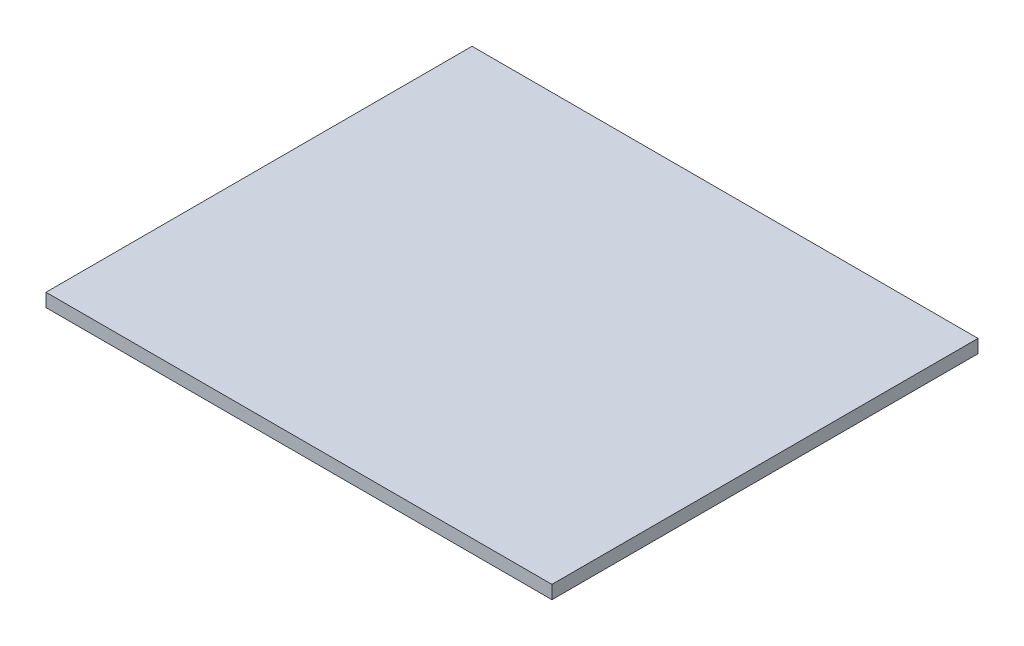
SolidWorks part; units mm, degrees
ref_plane "Front Plane" through (0, 0, 0) normal (0, 0, 1) x (1, 0, 0)
ref_plane "Top Plane" through (0, 0, 0) normal (0, 1, 0) x (1, 0, 0)
ref_plane "Right Plane" through (0, 0, 0) normal (1, 0, 0) x (0, 0, -1)
sketch "Sketch1" plane through (0, 0, 0) normal (0, 1, 0) x (1, 0, 0)
  line L0 (0, 0) -> (0, 32)
  line L1 (0, 0) -> (38, 0)
  line L2 (0, 32) -> (38, 32)
  line L3 (38, 0) -> (38, 32)
  line L4 (0, 0) -> (0, 9.65)
  line L5 (0, 9.65) -> (0, 18.3074)
  line L6 (0, 32) -> (0, 22.15)
  line L7 (0, 9.65) -> (0, 22.15)
  line L8 (0, 9.65) -> (-7.3, 9.65)
  line L9 (0, 22.15) -> (-7.3, 22.15)
  line L10 (-7.3, 9.65) -> (-7.3, 22.15)
extrude "Boss-Extrude1" add sketch "Sketch1" along normal blind 1 contours L1 L3 L2 L0
sketch "Sketch2" plane through (0, 1, 0) normal (0, 1, 0) x (1, 0, 0)
  line L0 (38, 32) -> (35.86, 32)
  line L1 (0, 32) -> (38, 32) construction
  line L2 (35.86, 32) -> (35.86, 0)
  line L3 (0, 0) -> (38, 0) construction
  line L4 (35.86, 32) -> (35.86, 29.85)
  line L5 (35.86, 0) -> (35.86, 2.25)
  line L6 (35.86, 2.25) -> (35.86, 29.85)
  line L7 (35.86, 2.25) -> (8.36, 2.25)
  line L8 (35.86, 29.85) -> (8.36, 29.85)
  line L9 (8.36, 2.25) -> (8.36, 29.85)
